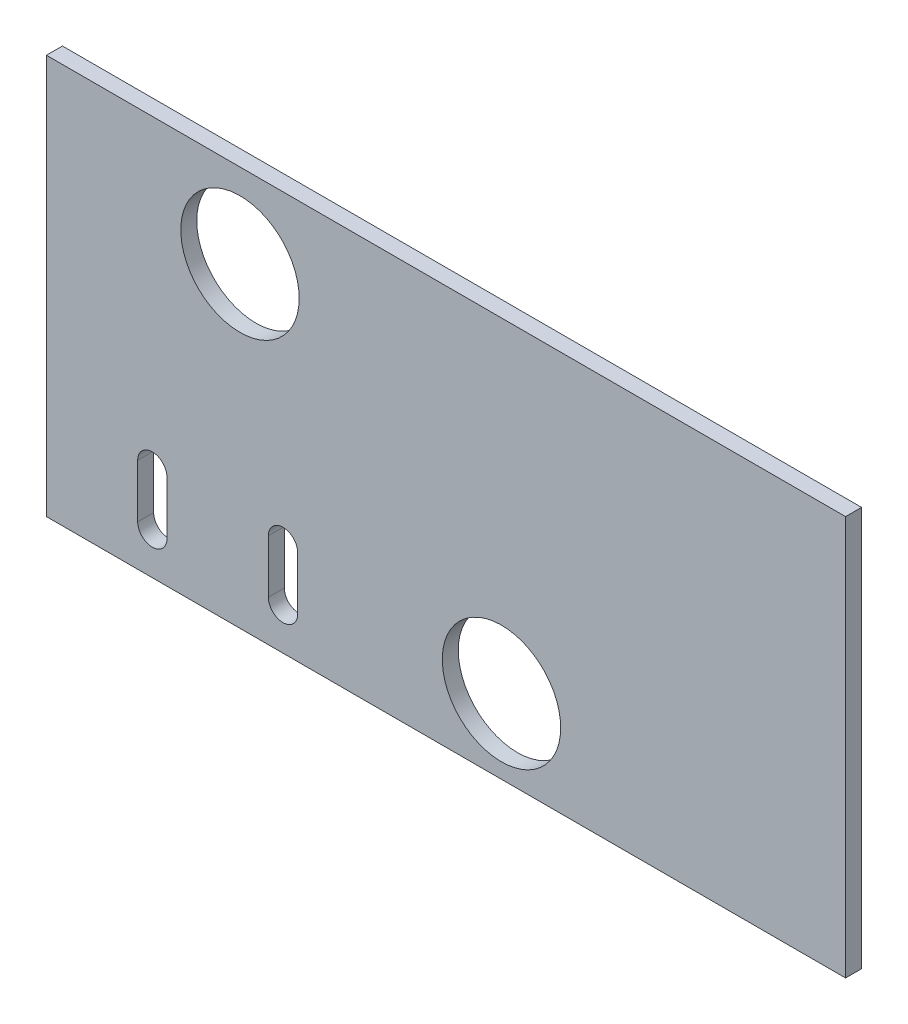
SolidWorks part; units mm, degrees
ref_plane "Front Plane" through (0, 0, 0) normal (0, 0, 1) x (1, 0, 0)
ref_plane "Top Plane" through (0, 0, 0) normal (0, 1, 0) x (1, 0, 0)
ref_plane "Right Plane" through (0, 0, 0) normal (1, 0, 0) x (0, 0, -1)
sketch "Sketch1" plane through (0, 0, 0) normal (0, 0, 1) x (1, 0, 0)
  line L1 (0, 0) -> (150, 0)
  line L2 (0, 0) -> (0, 75)
  line L3 (0, 75) -> (150, 75)
  line L4 (150, 0) -> (150, 75)
  dimension "D1" = 150
  dimension "D2" = 75
extrude "Boss-Extrude1" add sketch "Sketch1" along normal blind 3
sketch "Sketch2" plane through (0, 0, 3) normal (0, 0, 1) x (1, 0, 0)
  line L0 (19.8753, 7.7184) -> (19.8753, 17.7184) construction
  line L1 (17.1253, 7.7184) -> (17.1253, 17.7184)
  line L2 (22.6253, 7.7184) -> (22.6253, 17.7184)
  line L3 (44.4066, 7.7184) -> (44.4066, 17.7184) construction
  line L4 (41.6566, 7.7184) -> (41.6566, 17.7184)
  line L5 (47.1566, 7.7184) -> (47.1566, 17.7184)
  circle A0 centre (36.3279, 59.217) radius 11.11
  circle A1 centre (85.4136, 13.9491) radius 11.11
  arc A2 (17.1253, 7.7184) -> (22.6253, 7.7184) centre (19.8753, 7.7184) ccw
  arc A3 (22.6253, 17.7184) -> (17.1253, 17.7184) centre (19.8753, 17.7184) ccw
  arc A4 (41.6566, 7.7184) -> (47.1566, 7.7184) centre (44.4066, 7.7184) ccw
  arc A5 (47.1566, 17.7184) -> (41.6566, 17.7184) centre (44.4066, 17.7184) ccw
  point P6 (19.8753, 12.7184)
  point P11 (44.4066, 12.7184)
  dimension "D1" = 22.22
  dimension "D2" = 22.22
  dimension "D3" = 2.75
  dimension "D4" = 2.75
  dimension "D5" = 10
  dimension "D6" = 10
extrude "Cut-Extrude1" cut sketch "Sketch2" against normal blind 10
